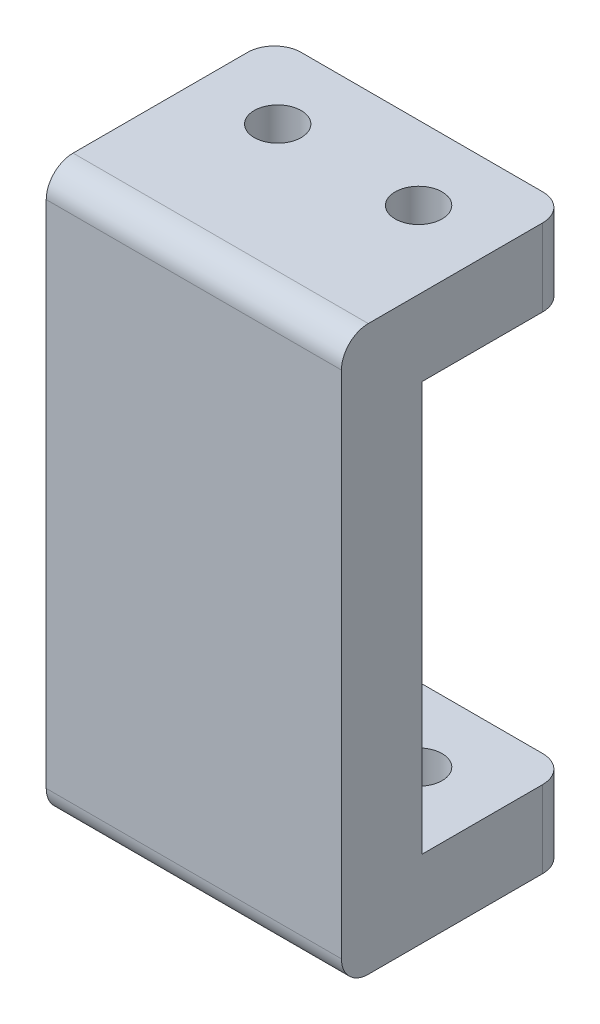
SolidWorks part; units mm, degrees
ref_plane "Front Plane" through (0, 0, 0) normal (0, 0, 1) x (1, 0, 0)
ref_plane "Top Plane" through (0, 0, 0) normal (0, 1, 0) x (1, 0, 0)
ref_plane "Right Plane" through (0, 0, 0) normal (1, 0, 0) x (0, 0, -1)
sketch "Sketch1" plane through (0, 0, 0) normal (0, 1, 0) x (1, 0, 0)
  line L0 (-5.25, 0) -> (5.25, 0) construction
  line L1 (-11, 5.5) -> (11, 5.5)
  line L2 (-11, 5.5) -> (-11, -5.5)
  line L3 (-11, -5.5) -> (11, -5.5)
  line L4 (11, 5.5) -> (11, -5.5)
  line L5 (0, -5.5) -> (0, 5.5) construction
  line L6 (-11, 0) -> (11, 0) construction
  line L8 (-11, -5.5) -> (11, -5.5)
  line L9 (-11, -5.5) -> (-11, -11.5)
  line L10 (-11, -11.5) -> (11, -11.5)
  line L11 (11, -5.5) -> (11, -11.5)
  line L12 (0, -11.5) -> (0, -5.5) construction
  line L13 (-11, -8.5) -> (11, -8.5) construction
  circle A0 centre (-5.25, 0) radius 1.75
  circle A1 centre (5.25, 0) radius 1.75
  point P0 (0, 0)
  point P7 (0, 0)
  point P273 (0, -8.5)
  dimension "D4" = 3.5
  dimension "D1" = 11
  dimension "D2" = 22
  dimension "D3" = 10.5
  dimension "D5" = 6
extrude "Boss-Extrude1" add sketch "Sketch1" along normal blind 42 contours L11 L3 L9 L10 | L4 L1 L2 L3 A1 A0
sketch "Sketch2" plane through (0, 0, -5.5) normal (0, 0, -1) x (-1, 0, 0)
  line L0 (11, 21) -> (-11, 21) construction
  line L1 (11, 42) -> (11, 0) construction
  line L2 (-11, 42) -> (-11, 0) construction
  line L4 (-11, 36.25) -> (11, 36.25)
  line L5 (-11, 36.25) -> (-11, 5.75)
  line L6 (-11, 5.75) -> (11, 5.75)
  line L7 (11, 36.25) -> (11, 5.75)
  line L8 (0, 5.75) -> (0, 36.25) construction
  line L9 (-11, 21) -> (11, 21) construction
  point P6 (0, 21)
  dimension "D1" = 30.5
extrude "Cut-Extrude1" cut sketch "Sketch2" against normal offset from surface (11 mm away) 6 up to face at (0, 21, 11.5)
fillet "Fillet1" radius 2 6 edges at (-11, 2.875, -5.5) (11, 2.875, -5.5) (11, 39.125, -5.5) (-11, 39.125, -5.5) (0, 42, 11.5) (0, 0, 11.5)
